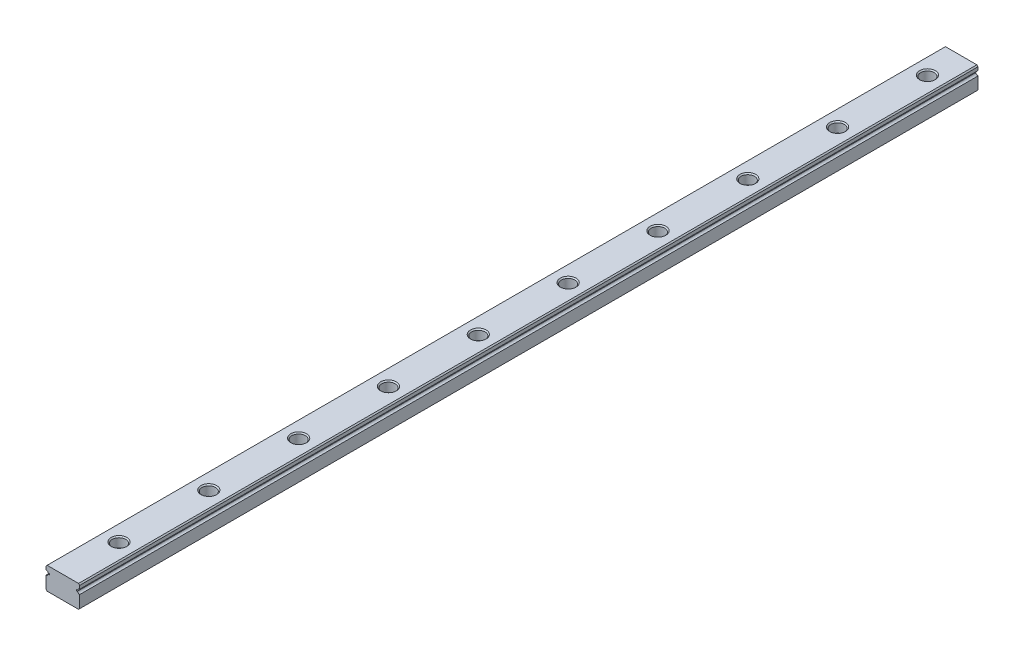
SolidWorks part; units mm, degrees
material "AISI 1035 鋼 (SS)"
ref_plane "Front Plane" through (0, 0, 0) normal (0, 0, 1) x (1, 0, 0)
ref_plane "Top Plane" through (0, 0, 0) normal (0, 1, 0) x (1, 0, 0)
ref_plane "Right Plane" through (0, 0, 0) normal (1, 0, 0) x (0, 0, -1)
sketch "Sketch1" plane through (0, 0, 0) normal (0, 0, 1) x (1, 0, 0)
  line L0 (-7.5, 0) -> (-7.5, 10) construction
  line L1 (-7.5, 10) -> (7.5, 10)
  line L2 (-7.5, 0) -> (7.5, 0)
  line L3 (-7.5, 10) -> (-7.5, 8.25)
  line L4 (-7.5, 8.25) -> (-6.5, 7.25) construction
  line L5 (-6.5, 7.25) -> (-6, 7.25)
  line L6 (-6.5, 6.75) -> (-7.5, 5.75) construction
  line L7 (-7.5, 5.75) -> (-7.5, 0)
  line L8 (-6, 7.25) -> (-6, 6.75)
  line L9 (-6, 6.75) -> (-6.5, 6.75)
  line L10 (-6.5, 6.75) -> (-6.25, 7) construction
  line L11 (-6.25, 7) -> (-6.5, 7.25) construction
  line L12 (-7.5, 8.25) -> (-7.5, 8.0308)
  line L13 (-7.5, 5.75) -> (-7.5, 5.9692)
  line L14 (0, 10) -> (0, 0) construction
  line L15 (6.25, 7) -> (6.5, 7.25) construction
  line L16 (6.5, 6.75) -> (6.25, 7) construction
  line L17 (6.5, 6.75) -> (7.5, 5.75) construction
  line L18 (7.5, 8.25) -> (6.5, 7.25) construction
  line L19 (7.5, 0) -> (7.5, 10) construction
  line L20 (7.5, 5.75) -> (7.5, 5.9692)
  line L21 (7.5, 8.25) -> (7.5, 8.0308)
  line L22 (6, 6.75) -> (6.5, 6.75)
  line L23 (6, 7.25) -> (6, 6.75)
  line L24 (7.5, 5.75) -> (7.5, 0)
  line L25 (6.5, 7.25) -> (6, 7.25)
  line L26 (7.5, 10) -> (7.5, 8.25)
  arc A0 (-7.5, 5.9692) -> (-6.5, 6.75) centre (-7.5, 7) ccw
  arc A1 (-6.5, 7.25) -> (-7.5, 8.0308) centre (-7.5, 7) ccw
  arc A2 (6.5, 7.25) -> (7.5, 8.0308) centre (7.5, 7) cw
  arc A3 (7.5, 5.9692) -> (6.5, 6.75) centre (7.5, 7) cw
  point P4 (-6, 7)
  point P28 (6, 7)
  dimension "D1" = 10
  dimension "D2" = 15
  dimension "D3" = 0.5
  dimension "D4" = 45
  dimension "D5" = 3
  dimension "D6" = 1.5
extrude "Boss-Extrude1" add sketch "Sketch1" along normal blind 400
chamfer "Chamfer1" distance 0.5 angle 45 4 edges at (-7.5, 0, 200) (7.5, 0, 200) (-7.5, 10, 200) (7.5, 10, 200)
hole_wizard "M3 六角承窩頭蓋螺釘的柱孔1" positions "3DSketch1" profile "Sketch3" counterbore size "M3" standard "ISO" end condition through all
sketch3d "3DSketch1"
  line L0 (0, 10, 0) -> (0, 10, 15) construction
  line L1 (7, 10, 0) -> (-7, 10, 0) construction
  point P0 (0, 10, 15)
  dimension "D1" = 15
sketch "Sketch3" plane through (0, 10, 15) normal (1, 0, 0) x (0, 0, 1)
  line L0 (0, 0) -> (0, 10)
  line L1 (1.75, 9.75) -> (2, 10)
  line L2 (3, 4.5) -> (1.75, 4.5)
  line L3 (1.75, 4.5) -> (1.75, 9.75)
  line L5 (3, 4.5) -> (3, 0.5)
  line L6 (3, 0.5) -> (3.5, 0)
  line L7 (3.5, 0) -> (0, 0)
  line L8 (-3, 0.5) -> (-3.5, 0) construction
  line L11 (0, -6.35) -> (0, 107.95) construction
  line L12 (2, 10) -> (0, 10)
  line L13 (-1.75, 9.75) -> (-2, 10) construction
  dimension "Thru Hole Dia." = 3.5
  dimension "Thru Hole Depth" = 10
  dimension "C'Bore Dia." = 6
  dimension "C'Bore Depth" = 4.5
  dimension "Near C'Sink Dia." = 7
  dimension "Near C'Sink Angle" = 90
  dimension "Far C'Sink Dia." = 4
  dimension "Far C'Sink Angle" = 90
pattern_linear "LPattern1" count 10 spacing 40 along (0, 0, 1) of "M3 六角承窩頭蓋螺釘的柱孔1"
